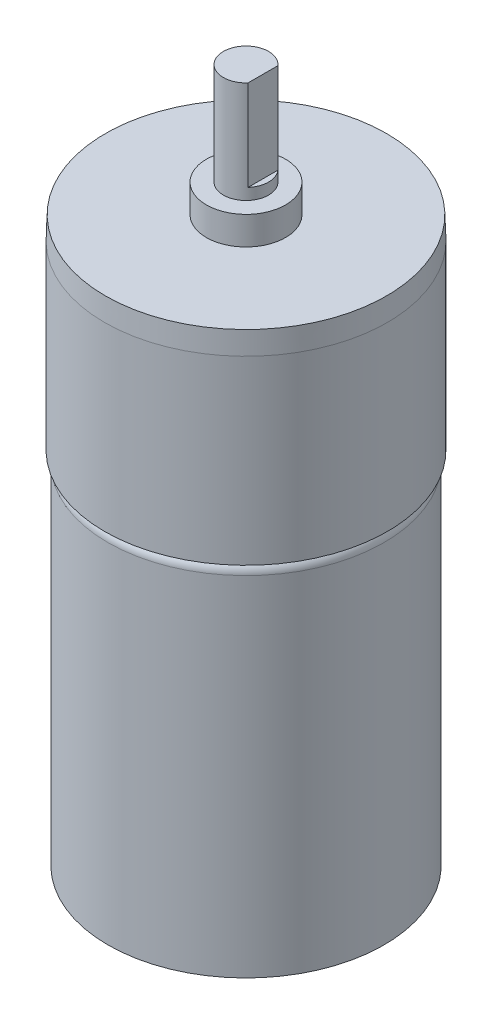
SolidWorks part; units mm, degrees
ref_plane "Front Plane" through (0, 0, 0) normal (0, 0, 1) x (1, 0, 0)
ref_plane "Top Plane" through (0, 0, 0) normal (0, 1, 0) x (1, 0, 0)
ref_plane "Right Plane" through (0, 0, 0) normal (1, 0, 0) x (0, 0, -1)
sketch "Sketch1" plane through (0, 0, 0) normal (0, 1, 0) x (1, 0, 0)
  circle A0 centre (0, 0) radius 12.2
extrude "Boss-Extrude1" add sketch "Sketch1" along normal blind 30.8 and the other way blind 1
fillet "Fillet2" radius 1 1 edges at (0, 30.8, 12.2)
sketch "Sketch4" plane through (0, 30.8, 0) normal (0, 1, 0) x (1, 0, 0)
  circle A0 centre (0, 0) radius 12.5
  dimension "D1" = 25
extrude "Boss-Extrude2" add sketch "Sketch4" along normal blind 18
chamfer "Chamfer5" distance 2 angle 2 1 edges at (0, 48.8, 12.5)
sketch "Sketch5" plane through (0, 48.8, 0) normal (0, 1, 0) x (1, 0, 0)
  circle A0 centre (0, 0) radius 3.5
extrude "Boss-Extrude3" add sketch "Sketch5" along normal blind 2.5
sketch "Sketch6" plane through (0, 51.3, 0) normal (0, 1, 0) x (1, 0, 0)
  circle A0 centre (0, 0) radius 2
  dimension "D1" = 4
extrude "Boss-Extrude4" add sketch "Sketch6" along normal blind 1
sketch "Sketch12" plane through (0, 52.3, 0) normal (0, 1, 0) x (1, 0, 0)
  line L0 (1.5, 1.3229) -> (1.5, -1.3229)
  arc A0 (1.5, 1.3229) -> (1.5, -1.3229) centre (0, 0) ccw
extrude "Boss-Extrude6" add sketch "Sketch12" along normal blind 8 contours A0 L0
